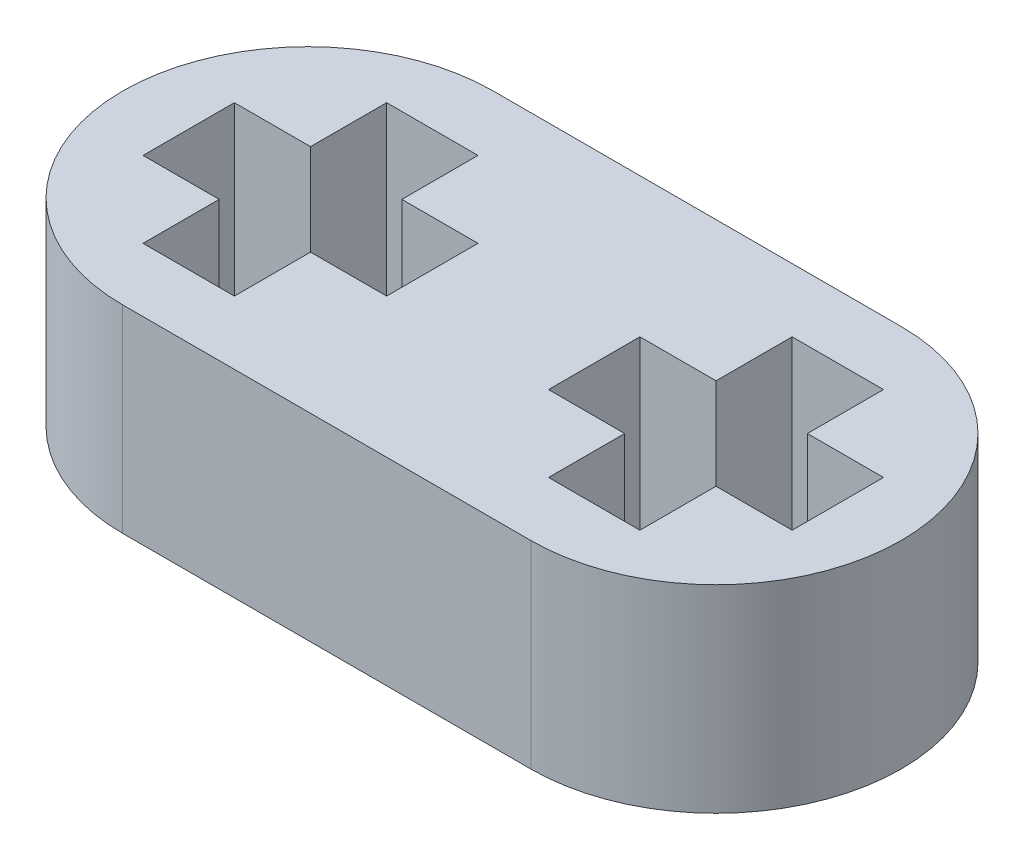
SolidWorks part; units mm, degrees
ref_plane "Front Plane" through (0, 0, 0) normal (0, 0, 1) x (1, 0, 0)
ref_plane "Top Plane" through (0, 0, 0) normal (0, 1, 0) x (1, 0, 0)
ref_plane "Right Plane" through (0, 0, 0) normal (1, 0, 0) x (0, 0, -1)
sketch "Sketch1" plane through (0, 0, 0) normal (0, 1, 0) x (1, 0, 0)
  line L0 (-4.02, 0) -> (4.02, 0) construction
  line L1 (-55, 0) -> (55, 0) construction
  line L2 (-4.02, 3.65) -> (4.02, 3.65)
  line L3 (-4.02, -3.65) -> (4.02, -3.65)
  line L4 (-7.67, 0) -> (-7.67, -5.5699) construction
  line L5 (-6.42, 0) -> (-6.42, -5.5699) construction
  line L6 (3.12, 2.4) -> (3.12, 0.9)
  line L7 (3.12, 2.4) -> (4.92, 2.4)
  line L8 (3.12, -2.4) -> (4.92, -2.4)
  line L9 (4.92, 2.4) -> (4.92, 0.9)
  line L10 (3.12, 2.4) -> (4.92, -2.4) construction
  line L11 (3.12, -2.4) -> (4.92, 2.4) construction
  line L12 (6.42, -0.9) -> (4.92, -0.9)
  line L13 (6.42, -0.9) -> (6.42, 0.9)
  line L14 (1.62, -0.9) -> (1.62, 0.9)
  line L15 (6.42, 0.9) -> (4.92, 0.9)
  line L16 (6.42, -0.9) -> (1.62, 0.9) construction
  line L17 (1.62, -0.9) -> (6.42, 0.9) construction
  line L18 (3.12, 0.9) -> (1.62, 0.9)
  line L19 (3.12, -0.9) -> (1.62, -0.9)
  line L20 (3.12, -0.9) -> (3.12, -2.4)
  line L21 (4.92, -0.9) -> (4.92, -2.4)
  line L34 (-4.8703, 2.4004) -> (-4.8703, 0.9004)
  line L35 (-4.8703, 2.4004) -> (-3.0703, 2.4004)
  line L36 (-4.8703, -2.3996) -> (-3.0703, -2.3996)
  line L37 (-3.0703, 2.4004) -> (-3.0703, 0.9004)
  line L38 (-1.5703, -0.8996) -> (-3.0703, -0.8996)
  line L39 (-1.5703, -0.8996) -> (-1.5703, 0.9004)
  line L40 (-6.3703, -0.8996) -> (-6.3703, 0.9004)
  line L41 (-1.5703, 0.9004) -> (-3.0703, 0.9004)
  line L42 (-4.8703, 0.9004) -> (-6.3703, 0.9004)
  line L43 (-4.8703, -0.8996) -> (-6.3703, -0.8996)
  line L44 (-4.8703, -0.8996) -> (-4.8703, -2.3996)
  line L45 (-3.0703, -0.8996) -> (-3.0703, -2.3996)
  line L46 (-4.8703, 0.9004) -> (-3.0703, -0.8996) construction
  line L47 (-3.9703, 0.0004) -> (-3.0703, 0.9004) construction
  arc A0 (-4.02, 3.65) -> (-4.02, -3.65) centre (-4.02, 0) ccw
  arc A1 (4.02, -3.65) -> (4.02, 3.65) centre (4.02, 0) ccw
  point P5 (0, 0)
  point P17 (4.02, 0)
  point P18 (4.02, 0)
  point P29 (7.67, 0)
  point P32 (6.42, 0)
  dimension "D3" = 1.25
  dimension "D5" = 8.04
  dimension "D1" = 7.3
  dimension "D2" = 15.34
  dimension "D4" = 1.25
extrude "Boss-Extrude1" add sketch "Sketch1" along normal blind 3.9
